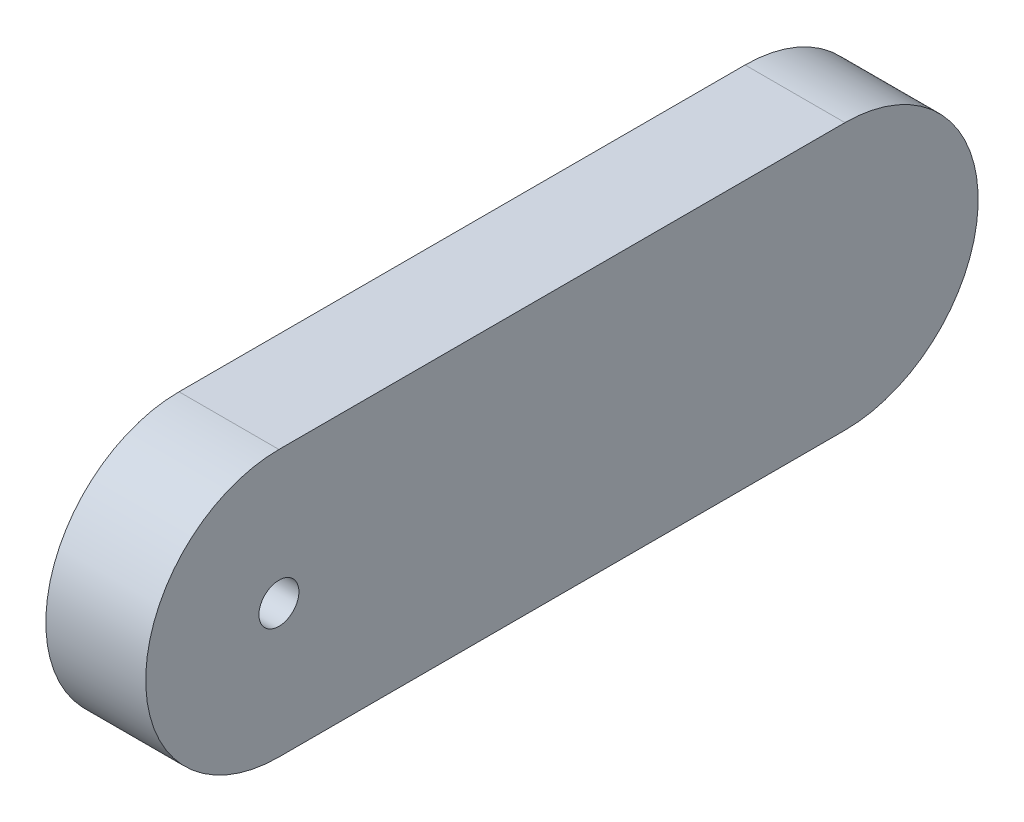
SolidWorks part; units mm, degrees
material "ABS"
ref_plane "Front Plane" through (0, 0, 0) normal (0, 0, 1) x (1, 0, 0)
ref_plane "Top Plane" through (0, 0, 0) normal (0, 1, 0) x (1, 0, 0)
ref_plane "Right Plane" through (0, 0, 0) normal (1, 0, 0) x (0, 0, -1)
sketch "Sketch2" plane through (0, 0, 0) normal (1, 0, 0) x (0, 0, -1)
  line L0 (0, 0) -> (0, 80)
  line L1 (0, 80) -> (250, 80)
  line L3 (250, 0) -> (0, 0)
  line L4 (250, 80) -> (250, 0)
  dimension "D1" = 80
  dimension "D4" = 250
extrude "Boss-Extrude1" add sketch "Sketch2" along normal blind 30
sketch "Sketch11" plane through (30, 0, 0) normal (1, 0, 0) x (0, 0, -1)
  line L0 (0, 40) -> (250, 40) construction
  line L1 (0, 80) -> (0, 0) construction
  line L2 (250, 0) -> (250, 80) construction
  circle A0 centre (40, 40) radius 6
  dimension "D1" = 40
  dimension "D2" = 12
extrude "Cut-Extrude2" cut sketch "Sketch11" against normal through all
sketch "Sketch14" plane through (0, 0, 0) normal (-1, 0, 0) x (0, 0, 1)
  line L0 (-250, 0) -> (-250, 80) construction
  arc A0 (-40, 0) -> (-40, 80) centre (-40, 40) ccw
  arc A1 (-210, 80) -> (-210, 0) centre (-210, 40) ccw
  dimension "D1" = 40
extrude "Cut-Extrude-Thin2" cut sketch "Sketch14" against normal through all thin
sketch "Sketch15" plane through (0, 0, 0) normal (-1, 0, 0) x (0, 0, 1)
  line L0 (-210, 80) -> (-40, 80) construction
  line L1 (-220, 50) -> (-180, 50)
  line L2 (-220, 50) -> (-220, 30)
  line L3 (-220, 30) -> (-180, 30)
  line L4 (-180, 50) -> (-180, 30)
  arc A0 (-210, 80) -> (-210, 0) centre (-210, 40) ccw construction
  dimension "D4" = 10
  dimension "D1" = 40
  dimension "D2" = 20
  dimension "D3" = 30
extrude "Cut-Extrude3" cut sketch "Sketch15" against normal blind 25
